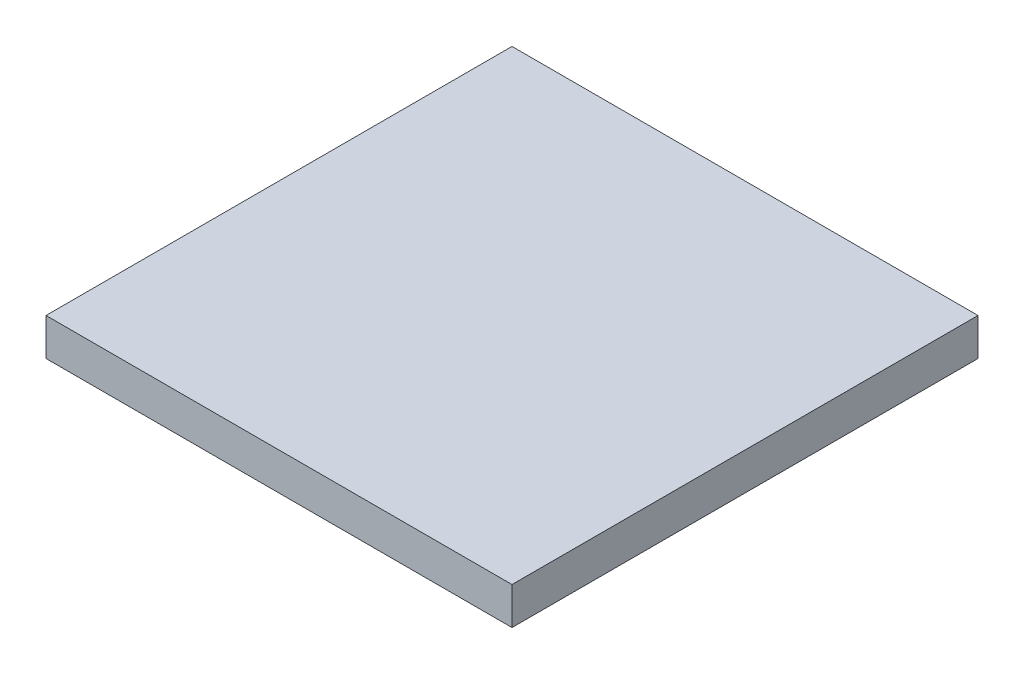
SolidWorks part; units mm, degrees
ref_plane "前视基准面" through (0, 0, 0) normal (0, 0, 1) x (1, 0, 0)
ref_plane "上视基准面" through (0, 0, 0) normal (0, 1, 0) x (1, 0, 0)
ref_plane "右视基准面" through (0, 0, 0) normal (1, 0, 0) x (0, 0, -1)
sketch "草图1" plane through (0, 0, 0) normal (0, 1, 0) x (1, 0, 0)
  line L1 (-12.5, 12.5) -> (12.5, 12.5)
  line L2 (-12.5, 12.5) -> (-12.5, -12.5)
  line L3 (-12.5, -12.5) -> (12.5, -12.5)
  line L4 (12.5, 12.5) -> (12.5, -12.5)
  line L5 (-12.5, 12.5) -> (12.5, -12.5) construction
  line L6 (-12.5, -12.5) -> (12.5, 12.5) construction
  point P0 (0, 0)
  dimension "D1" = 25
  dimension "D2" = 25
extrude "凸台-拉伸1" add sketch "草图1" along normal blind 2
